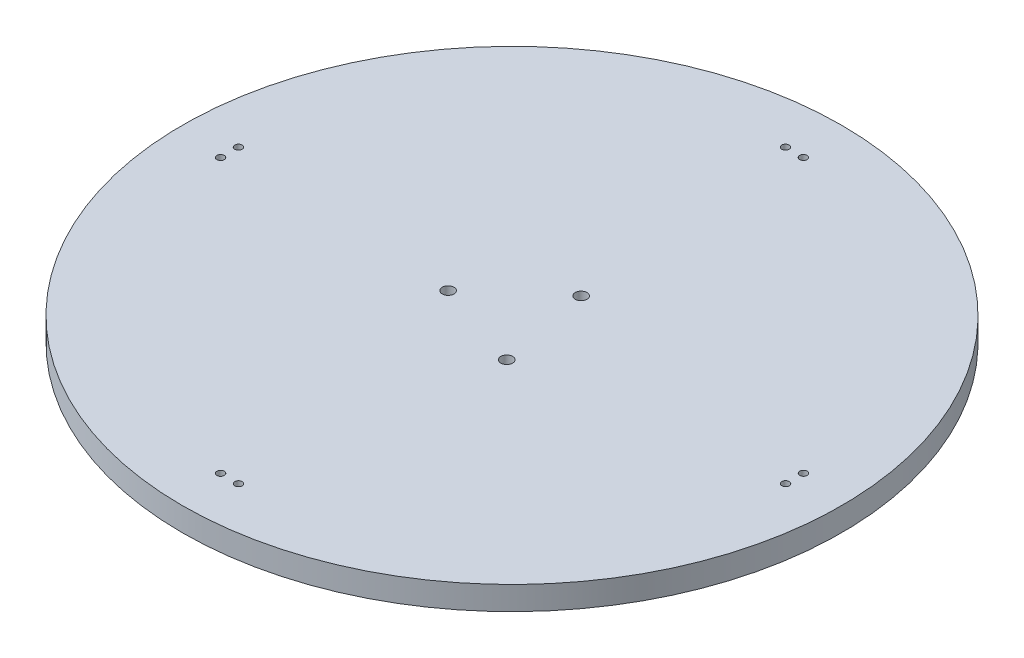
SolidWorks part; units mm, degrees
ref_plane "Front Plane" through (0, 0, 0) normal (0, 0, 1) x (1, 0, 0)
ref_plane "Top Plane" through (0, 0, 0) normal (0, 1, 0) x (1, 0, 0)
ref_plane "Right Plane" through (0, 0, 0) normal (1, 0, 0) x (0, 0, -1)
sketch "Sketch1" plane through (0, 0, 0) normal (0, 1, 0) x (1, 0, 0)
  circle A0 centre (0, 0) radius 88.9
  dimension "D1" = 177.8
extrude "Boss-Extrude1" add sketch "Sketch1" along normal blind 6.35
sketch "Sketch2" plane through (0, 0, 0) normal (0, -1, 0) x (1, 0, 0)
  line L0 (0, -88.9) -> (0, -41.3211) construction
  line L1 (2.4117, -76.2) -> (-2.4253, -76.2) construction
  circle A0 centre (2.4117, -76.2) radius 1
  circle A1 centre (-2.4253, -76.2) radius 1
  circle A2 centre (0, 0) radius 88.9 construction
  circle A3 centre (-76.2, -2.4117) radius 1
  circle A4 centre (-76.2, 2.4253) radius 1
  circle A5 centre (-2.4117, 76.2) radius 1
  circle A6 centre (2.4253, 76.2) radius 1
  circle A7 centre (76.2, 2.4117) radius 1
  circle A8 centre (76.2, -2.4253) radius 1
  point P24 (0, 0)
  dimension "D1" = 2
  dimension "D3" = 12.7
  dimension "D2" = 4
extrude "Cut-Extrude1" cut sketch "Sketch2" against normal up to next
sketch "Sketch4" plane through (0, 0, 0) normal (0, -1, 0) x (1, 0, 0)
  circle A0 centre (4.7668, -13.8858) radius 1.5875
  circle A1 centre (-14.4089, 2.8147) radius 1.5875
  circle A2 centre (9.642, 11.0711) radius 1.5875
  point P9 (0, 0)
  dimension "D1" = 3
extrude "Cut-Extrude2" cut sketch "Sketch4" against normal up to next
